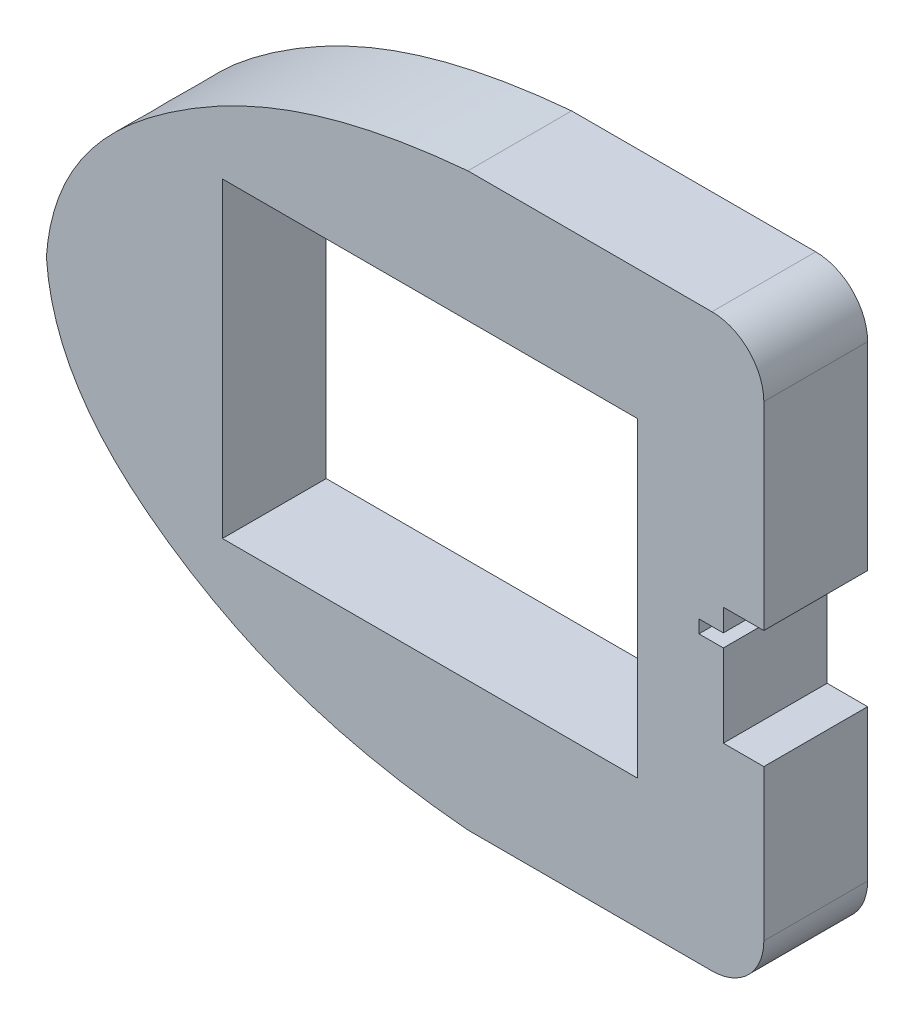
SolidWorks part; units mm, degrees
material "Polyurethane Foam Flexible"
ref_plane "Front Plane" through (0, 0, 0) normal (0, 0, 1) x (1, 0, 0)
ref_plane "Top Plane" through (0, 0, 0) normal (0, 1, 0) x (1, 0, 0)
ref_plane "Right Plane" through (0, 0, 0) normal (1, 0, 0) x (0, 0, -1)
sketch "Sketch1" plane through (0, 0, 0) normal (0, 0, 1) x (1, 0, 0)
  line L0 (-81.2118, 0) -> (81.2118, 0) construction
  line L1 (0, 79.4018) -> (0, 0) construction
  line L2 (0, 55) -> (47.0272, 55)
  line L3 (57.0272, 45) -> (57.0272, -45)
  line L4 (0.4417, -55) -> (47.0272, -55)
  arc A0 (0.4417, -55) -> (-0.4524, -54.9599) centre (0.4417, -45) cw
  arc A1 (57.0272, -45) -> (47.0272, -55) centre (47.0272, -45) cw
  arc A2 (57.0272, 45) -> (47.0272, 55) centre (47.0272, 45) ccw
  spline S0 degree 3 poles (-81.2118, 0) (-80.0302, 16.8295) (-64.3387, 33.147) (-33.3232, 49.9544) (-13.0594, 53.8599) (0, 55) knots 0 0 0 0 0.422844 0.624328 1 1 1 1
  spline S1 degree 3 poles (-81.2118, 0) (-80.0305, -16.8295) (-64.3384, -33.147) (-38.6518, -47.067) (-19.2356, -52.6556) (-6.2755, -54.4372) (-0.4524, -54.9599) knots 0 0 0 0 0.422833 0.624312 0.828189 0.995663 0.995663 0.995663 0.995663
  point P3 (0, 0)
  point P5 (-67.9177, 27.5126)
  point P7 (-81.2118, 0)
  point P8 (-80.3678, 5.9252)
  point P9 (-57.0907, 36.2609)
  point P10 (-38.4378, 46.3205)
  point P11 (-17.8892, 52.4557)
  point P12 (0, 55)
  point P14 (-76.013, 17.1802)
  point P22 (57.0272, 0)
  point P32 (57.0272, -55)
  point P35 (57.0272, 55)
  dimension "D2" = 10
  dimension "D1" = 110
extrude "Boss-Extrude1" add sketch "Sketch1" along normal blind 20
sketch "Sketch2" plane through (0, 0, 20) normal (0, 0, 1) x (1, 0, 0)
  line L0 (-81.2118, 0) -> (57.0272, 0) construction
  line L1 (57.0272, -45) -> (57.0272, 45) construction
  line L2 (32.7106, 30) -> (32.7106, -30)
  line L3 (32.7106, -30) -> (-47.2894, -30)
  line L4 (-47.2894, -30) -> (-47.2894, 30)
  line L5 (-47.2894, 30) -> (32.7106, 30)
  line L6 (-7.2894, 30) -> (-7.2894, -30) construction
  point P7 (32.7106, 0)
  dimension "D1" = 60
  dimension "D2" = 80
extrude "Cut-Extrude1" cut sketch "Sketch2" against normal blind 20
sketch "Sketch3" plane through (0, 0, 20) normal (0, 0, 1) x (1, 0, 0)
  line L0 (-34.5925, 0) -> (113.65, 0) construction
  line L1 (57.0272, 6.8) -> (49.2272, 6.8)
  line L2 (57.0272, -45) -> (57.0272, 45) construction
  line L3 (49.2272, 6.8) -> (49.2272, 2.5)
  line L4 (49.2272, -15.9) -> (57.0272, -15.9)
  line L5 (49.2272, 0) -> (44.5272, 0)
  line L6 (44.5272, 0) -> (44.5272, 2.5)
  line L7 (44.5272, 2.5) -> (49.2272, 2.5)
  line L8 (57.0272, 6.8) -> (57.0272, -15.9)
  line L9 (49.2272, 0) -> (49.2272, -15.9)
  dimension "D1" = 22.7
  dimension "D2" = 15.9
  dimension "D3" = 2.5
  dimension "D4" = 7.8
  dimension "D5" = 4.7
extrude "Cut-Extrude2" cut sketch "Sketch3" against normal blind 20
sketch "Sketch5" plane through (0, 2.5, 0) normal (0, -1, 0) x (1, 0, 0)
  line L0 (49.2272, 10) -> (-113.5416, 10) construction
  line L1 (49.2272, 0) -> (49.2272, 20) construction
  circle A0 centre (46.9272, 10) radius 1
  dimension "D1" = 2
  dimension "D2" = 2.3
extrude "Cut-Extrude4" cut sketch "Sketch5" against normal blind 1
